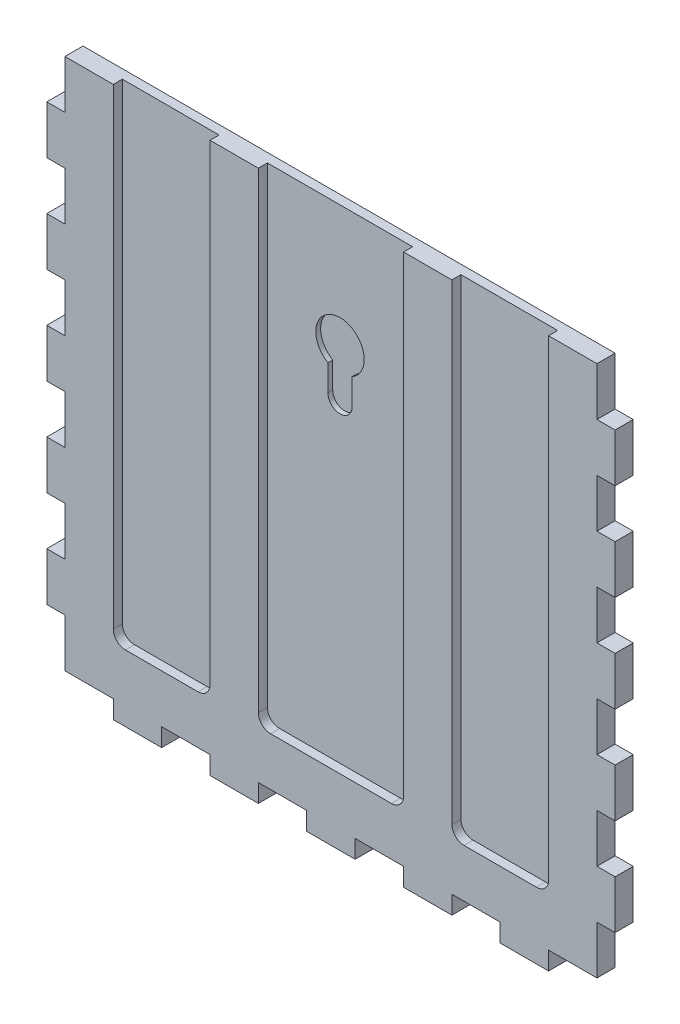
SolidWorks part; units mm, degrees
ref_plane "Front Plane" through (0, 0, 0) normal (0, 0, 1) x (1, 0, 0)
ref_plane "Top Plane" through (0, 0, 0) normal (0, 1, 0) x (1, 0, 0)
ref_plane "Right Plane" through (0, 0, 0) normal (1, 0, 0) x (0, 0, -1)
sketch "Sketch2" plane through (0, 0, 0) normal (0, 0, 1) x (1, 0, 0)
  line L1 (-139.7, -139.7) -> (139.7, -139.7)
  line L2 (-139.7, -139.7) -> (-139.7, 139.7)
  line L3 (-139.7, 139.7) -> (139.7, 139.7)
  line L4 (139.7, -139.7) -> (139.7, 139.7)
  line L5 (-139.7, -139.7) -> (139.7, 139.7) construction
  line L6 (-139.7, 139.7) -> (139.7, -139.7) construction
  point P0 (0, 0)
  dimension "D1" = 279.4
  dimension "D2" = 279.4
extrude "Boss-Extrude1" add sketch "Sketch2" along normal blind 9.525
sketch "Sketch3" plane through (0, 139.7, 0) normal (0, 1, 0) x (1, 0, 0)
  line L0 (-158.9087, 0) -> (158.9087, 0) construction
  line L1 (-114.3, -9.525) -> (-88.9, -9.525)
  line L2 (-114.3, -9.525) -> (-114.3, 0)
  line L3 (-114.3, 0) -> (-88.9, 0)
  line L4 (-88.9, -9.525) -> (-88.9, 0)
  line L6 (-139.7, -9.525) -> (-139.7, 0) construction
  dimension "D1" = 25.4
  dimension "D2" = 25.4
sketch "Sketch4" plane through (139.7, 0, 0) normal (1, 0, 0) x (0, 0, -1)
  line L0 (0, 158.9087) -> (0, -158.9087) construction
  line L1 (0, -114.3) -> (-9.525, -114.3)
  line L2 (0, -114.3) -> (0, -88.9)
  line L3 (0, -88.9) -> (-9.525, -88.9)
  line L4 (-9.525, -114.3) -> (-9.525, -88.9)
  line L5 (-9.525, -139.7) -> (-9.525, 139.7) construction
  line L7 (-9.525, -139.7) -> (0, -139.7) construction
  dimension "D1" = 25.4
  dimension "D2" = 25.4
extrude "Boss-Extrude3" add sketch "Sketch4" along normal blind 9.525
pattern_linear "LPattern2" count 5 spacing 50.8 along (0, 1, 0) of "Boss-Extrude3"
mirror "Mirror2" about plane through (0, 0, 0) normal (1, 0, 0) of "LPattern2", "Boss-Extrude3"
sketch "Sketch5" plane through (0, -139.7, 0) normal (0, -1, 0) x (1, 0, 0)
  line L1 (-114.3, 9.525) -> (-88.9, 9.525)
  line L2 (-114.3, 9.525) -> (-114.3, 0)
  line L3 (-114.3, 0) -> (-88.9, 0)
  line L4 (-88.9, 9.525) -> (-88.9, 0)
extrude "Boss-Extrude4" add sketch "Sketch5" along normal blind 9.525
pattern_linear "LPattern3" count 5 spacing 50.8 along (1, 0, 0) of "Boss-Extrude4"
sketch "Sketch6" plane through (0, 0, 9.525) normal (0, 0, 1) x (1, 0, 0)
  line L0 (139.7, 139.7) -> (-139.7, 139.7) construction
  line L1 (-38.1, 139.7) -> (38.1, 139.7)
  line L2 (-38.1, 139.7) -> (-38.1, -114.3)
  line L3 (-38.1, -114.3) -> (38.1, -114.3)
  line L4 (38.1, 139.7) -> (38.1, -114.3)
  line L5 (139.7, 114.3) -> (139.7, 139.7) construction
  line L6 (-114.3, 139.7) -> (-63.5, 139.7)
  line L7 (-114.3, 139.7) -> (-114.3, -114.3)
  line L8 (-114.3, -114.3) -> (-63.5, -114.3)
  line L9 (-63.5, 139.7) -> (-63.5, -114.3)
  line L10 (63.5, 139.7) -> (114.3, 139.7)
  line L11 (63.5, 139.7) -> (63.5, -114.3)
  line L12 (63.5, -114.3) -> (114.3, -114.3)
  line L13 (114.3, 139.7) -> (114.3, -114.3)
  line L14 (-139.7, 139.7) -> (-139.7, 114.3) construction
  point P19 (-114.3, -114.3)
  dimension "D1" = 254
  dimension "D2" = 25.4
  dimension "D3" = 25.4
  dimension "D4" = 25.4
  dimension "D5" = 25.4
  dimension "D6" = 254
  dimension "D7" = 254
  dimension "D8" = 38.1
  dimension "D9" = 38.1
extrude "Cut-Extrude1" cut sketch "Sketch6" against normal blind 4.7625
fillet "Fillet1" radius 6.35 6 edges at (114.3, -114.3, 7.1438) (63.5, -114.3, 7.1438) (38.1, -114.3, 7.1438) (-38.1, -114.3, 7.1438) (-63.5, -114.3, 7.1438) (-114.3, -114.3, 7.1438)
sketch "Sketch7" plane through (0, 0, 4.7625) normal (0, 0, 1) x (1, 0, 0)
  line L1 (6.35, 64.7113) -> (6.35, 51.0014)
  line L2 (-6.35, 64.7113) -> (-6.35, 51.0014)
  arc A0 (6.35, 64.7113) -> (-6.35, 64.7113) centre (0, 75.7098) ccw
  arc A2 (-6.35, 51.0014) -> (6.35, 51.0014) centre (0, 51.0014) ccw
  point P2 (0, 63.3556)
  dimension "D1" = 25.4
  dimension "D2" = 6.35
extrude "Cut-Extrude2" cut sketch "Sketch7" against normal blind 2.54
